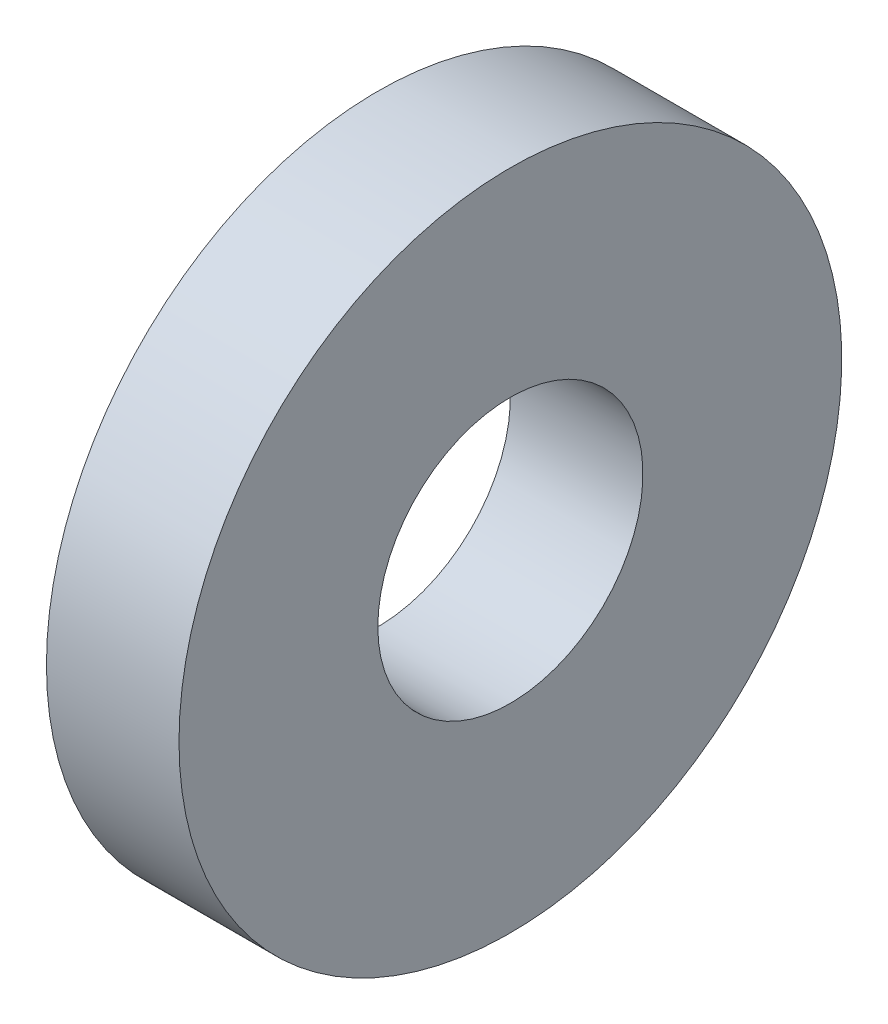
SolidWorks part; units mm, degrees
ref_plane "Front Plane" through (0, 0, 0) normal (0, 0, 1) x (1, 0, 0)
ref_plane "Top Plane" through (0, 0, 0) normal (0, 1, 0) x (1, 0, 0)
ref_plane "Right Plane" through (0, 0, 0) normal (1, 0, 0) x (0, 0, -1)
sketch "Sketch1" plane through (0, 0, 0) normal (0, 0, 1) x (1, 0, 0)
  line L0 (0, 0) -> (0, 13.7066) construction
  line L1 (0, 0) -> (9.446, 0) construction
  line L4 (2.5, 12.5) -> (-2.5, 12.5)
  line L5 (2.5, 12.5) -> (2.5, 5)
  line L6 (2.5, 5) -> (-2.5, 5)
  line L7 (-2.5, 12.5) -> (-2.5, 5)
  point P3 (0, 4.5089)
  point P4 (0, 0)
  point P9 (0, 4.5089)
  point P11 (2.974, 12.5)
  dimension "D1" = 5
  dimension "D2" = 5
  dimension "D3" = 25
revolve "Revolve4" add sketch "Sketch1" angle 360 about L1
